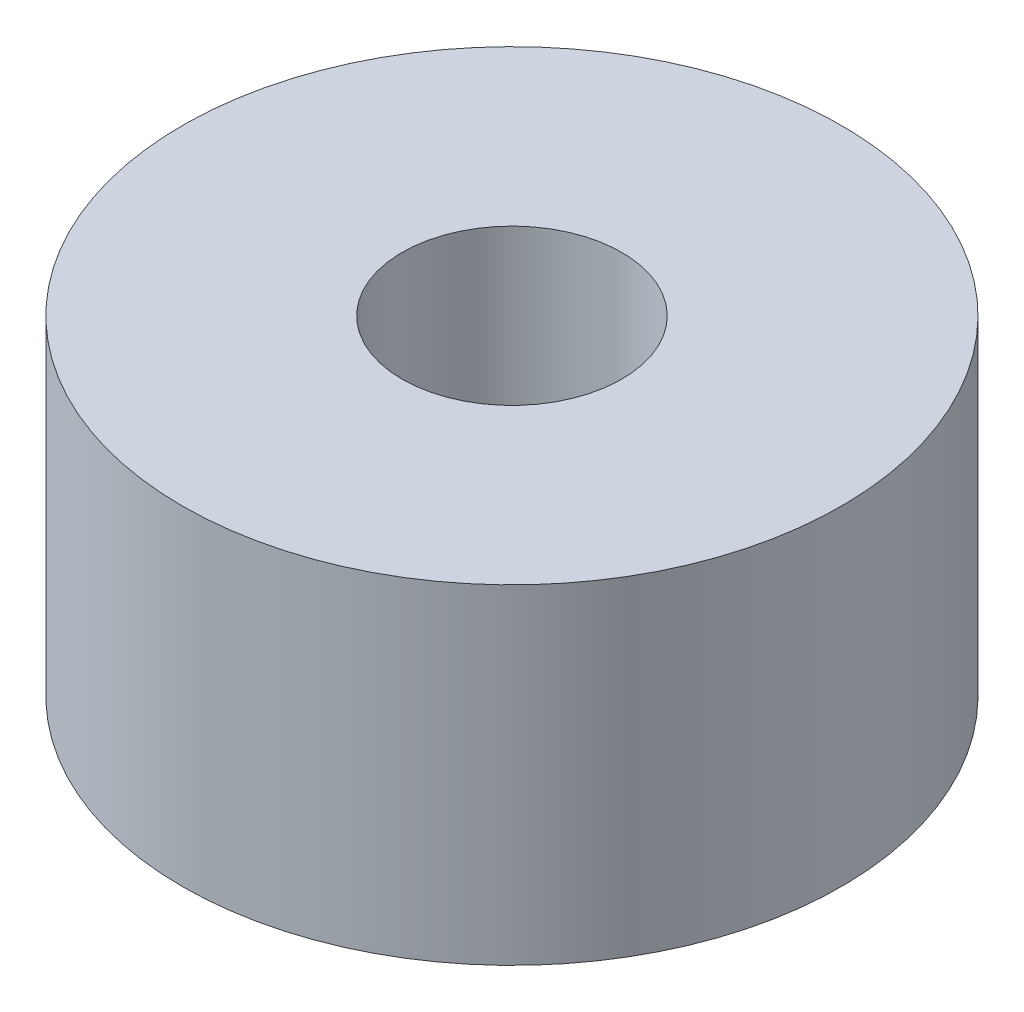
SolidWorks part; units mm, degrees
ref_plane "前视基准面" through (0, 0, 0) normal (0, 0, 1) x (1, 0, 0)
ref_plane "上视基准面" through (0, 0, 0) normal (0, 1, 0) x (1, 0, 0)
ref_plane "右视基准面" through (0, 0, 0) normal (1, 0, 0) x (0, 0, -1)
other "Configuration Table"
sketch "草图1" plane through (0, 0, 0) normal (0, 1, 0) x (1, 0, 0)
  circle A0 centre (0, 0) radius 3
  circle A1 centre (0, 0) radius 1
  dimension "D1" = 6
  dimension "D2" = 2
extrude "凸台-拉伸1" add sketch "草图1" along normal blind 3
